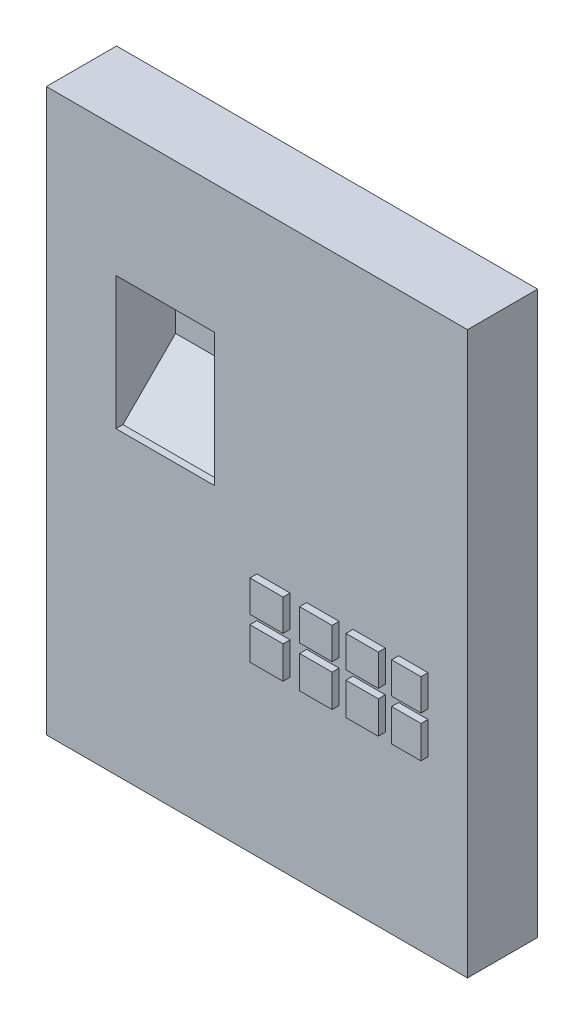
SolidWorks part; units mm, degrees
ref_plane "Alzado" through (0, 0, 0) normal (0, 0, 1) x (1, 0, 0)
ref_plane "Planta" through (0, 0, 0) normal (0, 1, 0) x (1, 0, 0)
ref_plane "Vista lateral" through (0, 0, 0) normal (1, 0, 0) x (0, 0, -1)
sketch "Croquis1" plane through (0, 0, 0) normal (0, 0, 1) x (1, 0, 0)
  line L1 (0, 0) -> (120, 0)
  line L2 (0, 0) -> (0, -160)
  line L3 (0, -160) -> (120, -160)
  line L4 (120, 0) -> (120, -160)
  dimension "D1" = 120
  dimension "D2" = 160
extrude "Saliente-Extruir1" add sketch "Croquis1" along normal blind 20
sketch "Croquis2" plane through (0, 0, 20) normal (0, 0, 1) x (1, 0, 0)
  line L1 (19.8164, -74.5204) -> (47.9664, -74.5204)
  line L2 (19.8164, -74.5204) -> (19.8164, -36.7006)
  line L3 (19.8164, -36.7006) -> (47.9664, -36.7006)
  line L4 (47.9664, -74.5204) -> (47.9664, -36.7006)
extrude "Cortar-Extruir1" cut sketch "Croquis2" against normal blind 17
chamfer "Chaflán1" distance 15 angle 45 1 edges at (33.8914, -74.5204, 3)
sketch "Croquis3" plane through (0, 0, 20) normal (0, 0, 1) x (1, 0, 0)
  line L1 (60, -101.8109) -> (69.455, -101.8109)
  line L2 (60, -101.8109) -> (60, -111.051)
  line L3 (60, -111.051) -> (69.455, -111.051)
  line L4 (69.455, -101.8109) -> (69.455, -111.051)
  line L5 (74.1824, -101.8109) -> (83.4225, -101.8109)
  line L6 (74.1824, -101.8109) -> (74.1824, -111.051)
  line L7 (74.1824, -111.051) -> (83.4225, -111.051)
  line L8 (83.4225, -101.8109) -> (83.4225, -111.051)
  line L9 (87.3683, -101.8109) -> (96.5835, -101.8109)
  line L10 (87.3683, -101.8109) -> (87.3683, -111.051)
  line L11 (87.3683, -111.051) -> (96.5835, -111.051)
  line L12 (96.5835, -101.8109) -> (96.5835, -111.051)
  line L13 (100.3924, -101.8109) -> (108.7475, -101.8109)
  line L14 (100.3924, -101.8109) -> (100.3924, -111.051)
  line L15 (100.3924, -111.051) -> (108.7475, -111.051)
  line L16 (108.7475, -101.8109) -> (108.7475, -111.051)
  line L17 (60, -90.2708) -> (69.455, -90.2708)
  line L18 (60, -90.2708) -> (60, -99.2403)
  line L19 (60, -99.2403) -> (69.455, -99.2403)
  line L20 (69.455, -90.2708) -> (69.455, -99.2403)
  line L21 (74.1824, -90.2708) -> (83.4225, -90.2708)
  line L22 (74.1824, -90.2708) -> (74.1824, -99.2403)
  line L23 (74.1824, -99.2403) -> (83.4225, -99.2403)
  line L24 (83.4225, -90.2708) -> (83.4225, -99.2403)
  line L25 (87.3683, -90.2708) -> (96.5835, -90.2708)
  line L26 (87.3683, -90.2708) -> (87.3683, -99.2403)
  line L27 (87.3683, -99.2403) -> (96.5835, -99.2403)
  line L28 (96.5835, -90.2708) -> (96.5835, -99.2403)
  line L29 (100.3924, -90.2708) -> (108.7475, -90.2708)
  line L30 (100.3924, -90.2708) -> (100.3924, -99.2403)
  line L31 (100.3924, -99.2403) -> (108.7475, -99.2403)
  line L32 (108.7475, -90.2708) -> (108.7475, -99.2403)
extrude "Saliente-Extruir2" add sketch "Croquis3" along normal blind 2
